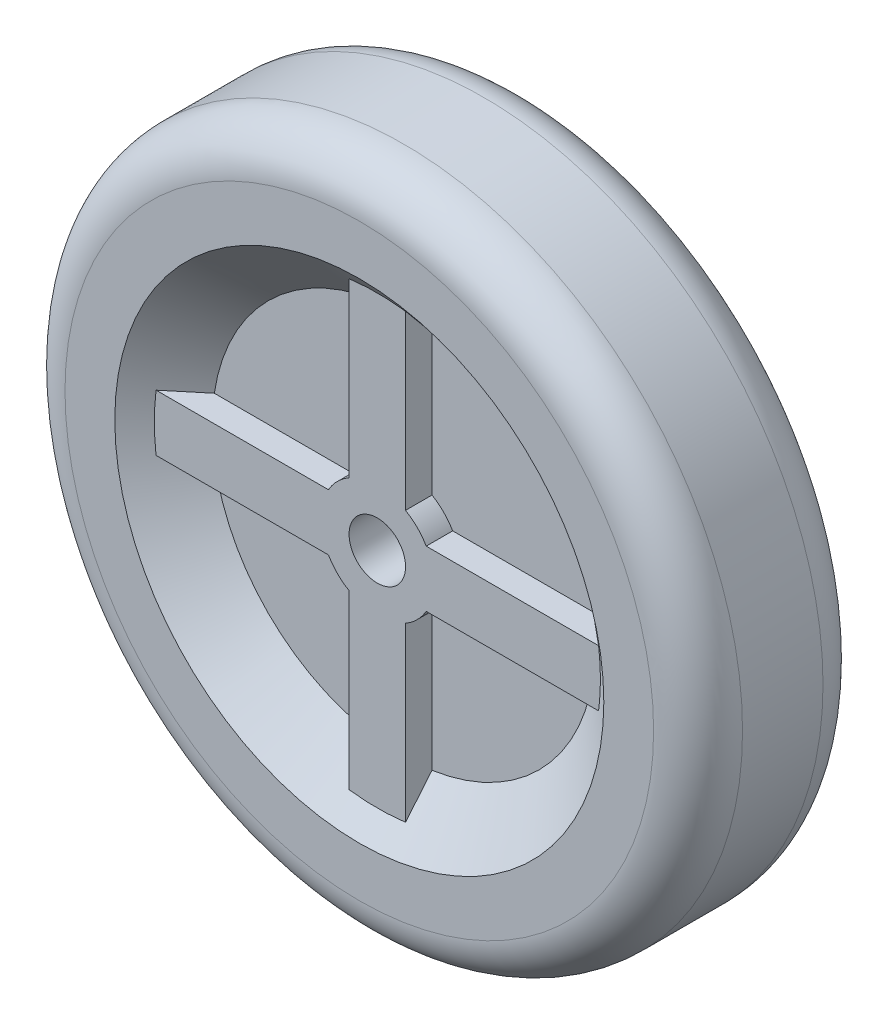
SolidWorks part; units mm, degrees
ref_plane "Front Plane" through (0, 0, 0) normal (0, 0, 1) x (1, 0, 0)
ref_plane "Top Plane" through (0, 0, 0) normal (0, 1, 0) x (1, 0, 0)
ref_plane "Right Plane" through (0, 0, 0) normal (1, 0, 0) x (0, 0, -1)
sketch "Sketch1" plane through (0, 0, 0) normal (0, 0, 1) x (1, 0, 0)
  circle A0 centre (0, 0) radius 76.2
  dimension "D1" = 152.4
extrude "Boss-Extrude1" add sketch "Sketch1" along normal blind 38.1
fillet "Fillet1" radius 10 2 edges at (76.2, 0, 0) (76.2, 0, 38.1)
sketch "Sketch2" plane through (0, 0, 38.1) normal (0, 0, 1) x (1, 0, 0)
  circle A0 centre (0, 0) radius 6.35
  dimension "D1" = 12.7
extrude "Cut-Extrude1" cut sketch "Sketch2" against normal blind 38.1
sketch "Sketch3" plane through (0, 0, 38.1) normal (0, 0, 1) x (1, 0, 0)
  circle A0 centre (0, 0) radius 55
  dimension "D1" = 110
extrude "Cut-Extrude2" cut sketch "Sketch3" against normal blind 10 draft 50
ref_plane "Plane1" through (0, 0, 19.05) normal (0, 0, -1) x (-1, 0, 0)
mirror "Mirror1" about plane through (0, 0, 19.05) normal (0, 0, -1) of "Cut-Extrude2"
sketch "Sketch4" plane through (0, 0, 19.05) normal (0, 0, -1) x (-1, 0, 0)
  line L0 (10.9985, 6.35) -> (54.6322, 6.35)
  line L2 (-6.35, 10.9985) -> (-6.35, 54.6322)
  line L3 (-6.35, 54.6322) -> (6.35, 54.6322)
  line L4 (6.35, 10.9985) -> (6.35, 54.6322)
  line L5 (54.6322, 6.35) -> (54.6322, -6.35)
  line L6 (10.9985, -6.35) -> (54.6322, -6.35)
  line L8 (6.35, -10.9985) -> (6.35, -54.6322)
  line L9 (6.35, -54.6322) -> (-6.35, -54.6322)
  line L10 (-6.35, -10.9985) -> (-6.35, -54.6322)
  line L12 (-10.9985, -6.35) -> (-54.6322, -6.35)
  line L13 (-54.6322, -6.35) -> (-54.6322, 6.35)
  line L14 (-10.9985, 6.35) -> (-54.6322, 6.35)
  arc A0 (-6.35, 10.9985) -> (-10.9985, 6.35) centre (0, 0) ccw
  circle A1 centre (0, 0) radius 6.35
  circle A2 centre (0, 0) radius 55 construction
  arc A3 (-10.9985, -6.35) -> (-6.35, -10.9985) centre (0, 0) ccw
  arc A4 (6.35, -10.9985) -> (10.9985, -6.35) centre (0, 0) ccw
  arc A5 (10.9985, 6.35) -> (6.35, 10.9985) centre (0, 0) ccw
  point P25 (0, 0)
  dimension "D1" = 25.4
  dimension "D2" = 4
extrude "Boss-Extrude3" add sketch "Sketch4" along normal mid plane 30
